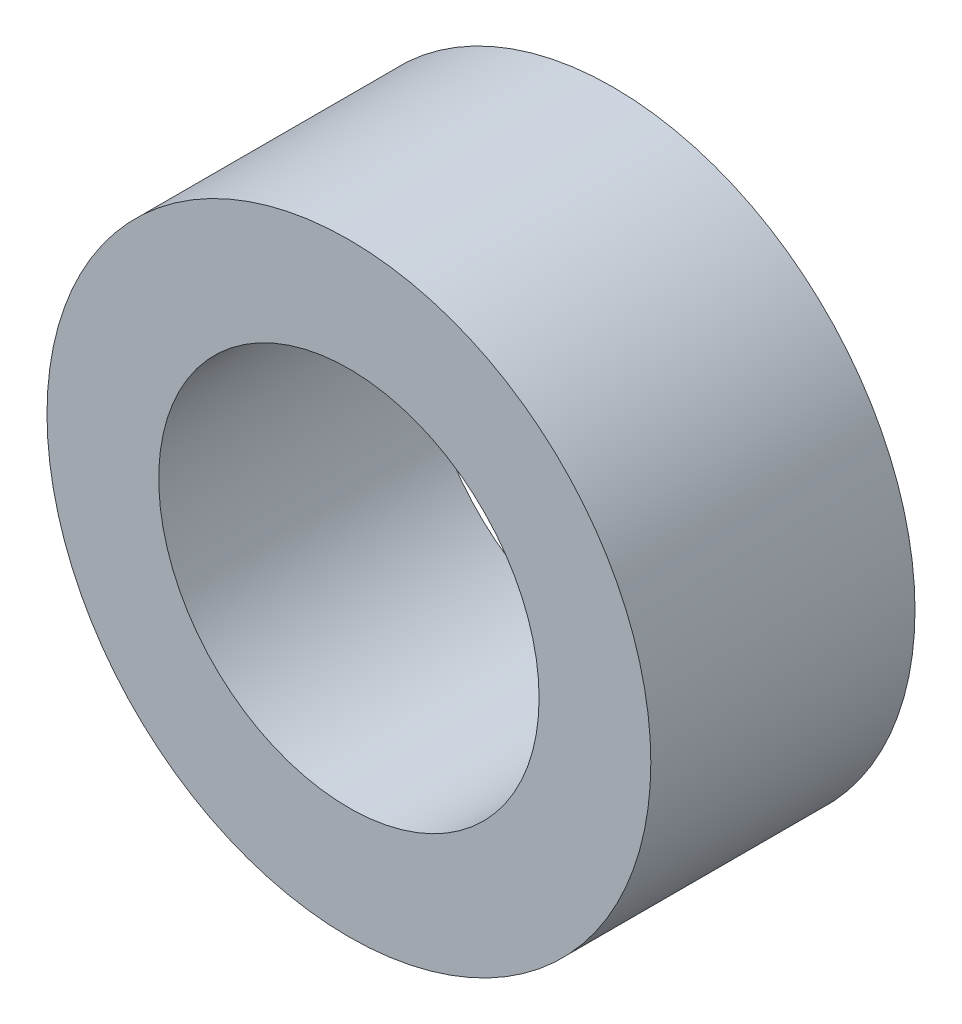
SolidWorks part; units mm, degrees
material "POLYURETHANE (11671)"
ref_plane "Front Plane" through (0, 0, 0) normal (0, 0, 1) x (1, 0, 0)
ref_plane "Top Plane" through (0, 0, 0) normal (0, 1, 0) x (1, 0, 0)
ref_plane "Right Plane" through (0, 0, 0) normal (1, 0, 0) x (0, 0, -1)
sketch "Sketch2" plane through (0, 0, 4) normal (0, 0, 1) x (1, 0, 0)
  circle A0 centre (216.0509, 692.6424) radius 4 construction
  circle A1 centre (216.0509, 692.6424) radius 4
  circle A2 centre (216.0509, 692.6424) radius 6.35
  dimension "D1" = 12.7
extrude "Boss-Extrude1" add sketch "Sketch2" along normal blind 5.5562
